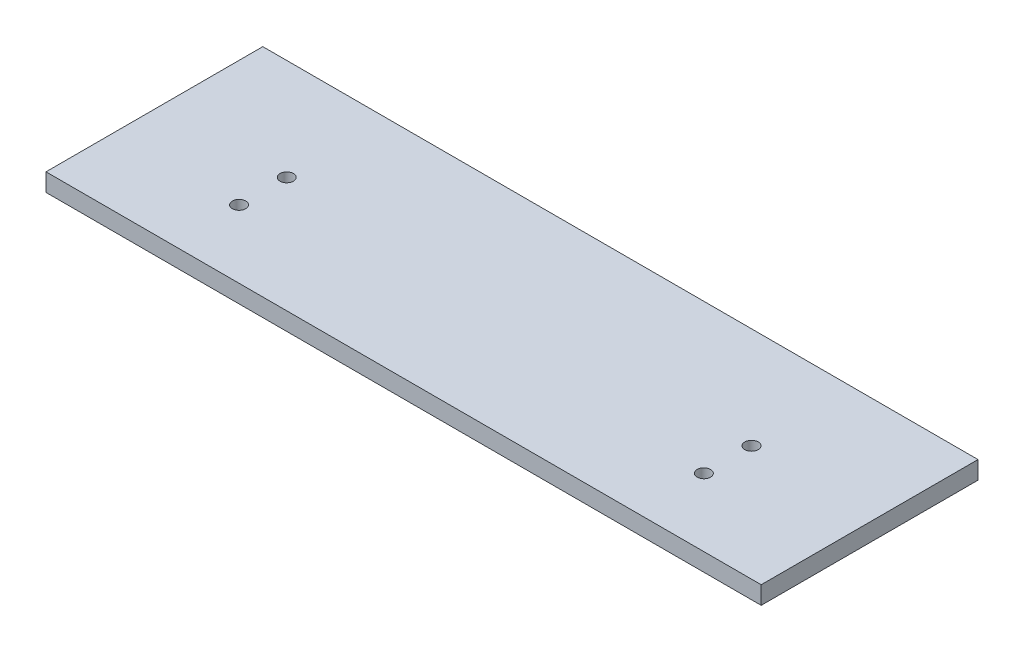
SolidWorks part; units mm, degrees
ref_plane "Front Plane" through (0, 0, 0) normal (0, 0, 1) x (1, 0, 0)
ref_plane "Top Plane" through (0, 0, 0) normal (0, 1, 0) x (1, 0, 0)
ref_plane "Right Plane" through (0, 0, 0) normal (1, 0, 0) x (0, 0, -1)
sketch "Sketch1" plane through (0, 0, 0) normal (0, 1, 0) x (1, 0, 0)
  line L0 (-193.2984, 139.7432) -> (-155.1984, 139.7432) construction
  line L1 (-193.2984, 177.8432) -> (314.7016, 177.8432)
  line L2 (-193.2984, 177.8432) -> (-193.2984, 23.8433)
  line L3 (-193.2984, 23.8433) -> (314.7016, 23.8433)
  line L4 (314.7016, 177.8432) -> (314.7016, 23.8433)
  line L5 (-155.1984, 139.7432) -> (-155.1984, 177.8432) construction
  line L6 (-155.1984, 139.7432) -> (-155.1984, 38.224) construction
  line L7 (-155.1984, 38.224) -> (-53.5984, 38.224) construction
  line L8 (-53.5984, 38.224) -> (-53.5984, 139.8454) construction
  line L9 (-53.5984, 139.8454) -> (-155.1984, 139.7432) construction
  line L10 (314.7016, 139.7432) -> (276.6016, 139.7432) construction
  line L11 (276.6016, 139.7432) -> (276.6016, 177.8432) construction
  line L12 (276.6016, 139.7432) -> (175.0016, 139.7432) construction
  line L13 (175.0016, 139.7432) -> (175.0016, 38.1432) construction
  line L14 (175.0016, 38.1432) -> (276.6016, 38.1432) construction
  line L15 (276.6016, 139.7432) -> (276.6016, 38.1432) construction
  line L16 (225.8016, 139.7432) -> (225.8016, 38.1432) construction
  line L17 (-104.3984, 139.7943) -> (-104.3984, 38.224) construction
  line L18 (-104.3984, 139.7943) -> (-104.3984, 105.9276) construction
  line L19 (-104.3984, 38.224) -> (-104.3984, 72.0907) construction
  line L20 (225.8016, 139.7432) -> (225.8016, 105.8766) construction
  line L21 (225.8016, 38.1432) -> (225.8016, 72.0099) construction
  circle A0 centre (-104.3984, 105.9276) radius 4.7625
  circle A1 centre (-104.3984, 72.0907) radius 4.7625
  circle A2 centre (225.8016, 105.8766) radius 4.7625
  circle A3 centre (225.8016, 72.0099) radius 4.7625
  dimension "D3" = 48.2474
  dimension "D1" = 508
  dimension "D2" = 153.9999
  dimension "D4" = 50.8
  dimension "D5" = 71.9156
extrude "Boss-Extrude1" add sketch "Sketch1" along normal blind 12.7
